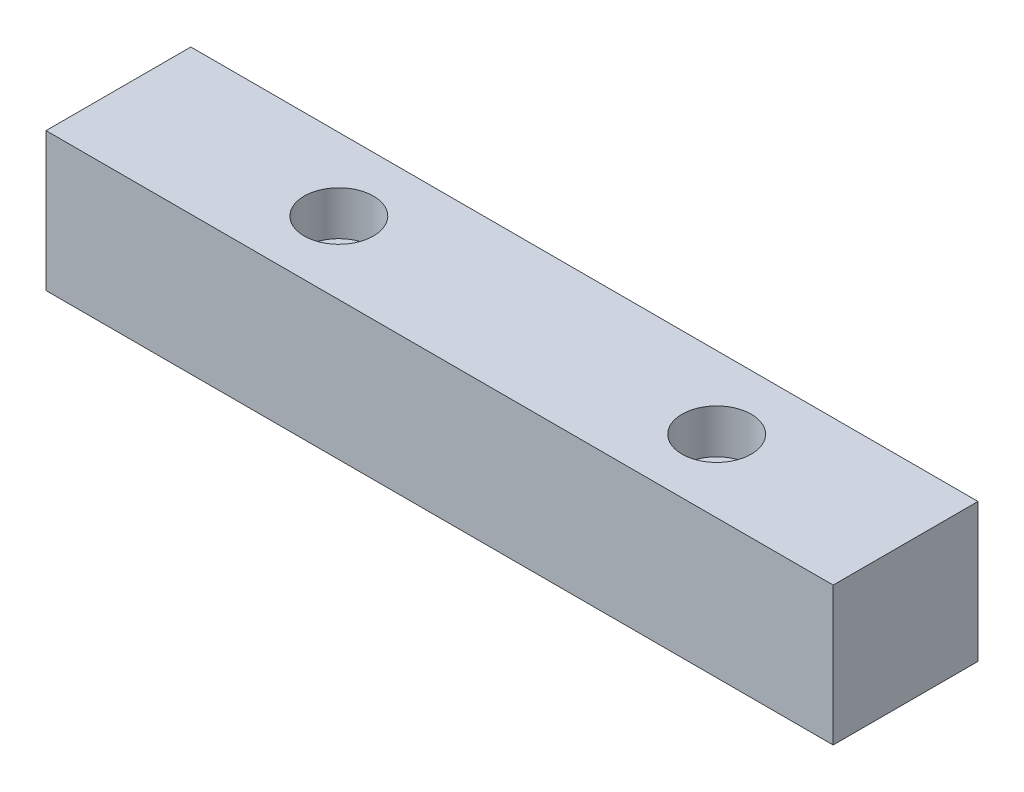
SolidWorks part; units mm, degrees
material "A3钢"
ref_plane "前视基准面" through (0, 0, 0) normal (0, 0, 1) x (1, 0, 0)
ref_plane "上视基准面" through (0, 0, 0) normal (0, 1, 0) x (1, 0, 0)
ref_plane "右视基准面" through (0, 0, 0) normal (1, 0, 0) x (0, 0, -1)
sketch "草图1" plane through (0, 0, 0) normal (1, 0, 0) x (0, 0, -1)
  line L1 (-11.5, -11) -> (11.5, -11)
  line L2 (-11.5, -11) -> (-11.5, 11)
  line L3 (-11.5, 11) -> (11.5, 11)
  line L4 (11.5, -11) -> (11.5, 11)
  line L5 (-11.5, -11) -> (11.5, 11) construction
  line L6 (-11.5, 11) -> (11.5, -11) construction
  point P0 (0, 0)
  dimension "D1" = 22
  dimension "D2" = 23
extrude "凸台-拉伸1" add sketch "草图1" along normal blind 125
hole_wizard "打孔尺寸(%根据)内六角圆柱头螺钉的类型1" positions "草图2" profile "草图3" counterbore size "M6" standard "GB" end condition through all
sketch "草图2" plane through (0, 11, 0) normal (0, 1, 0) x (1, 0, 0)
  line L0 (0, 11.5) -> (0, -11.5) construction
  line L1 (-4.5209, 0) -> (108.6401, 0) construction
  point P0 (35, 0)
  dimension "D1" = 35
sketch "草图3" plane through (35, 11, 0) normal (1, 0, 0) x (0, 0, 1)
  line L0 (0, 0) -> (0, 22)
  line L1 (0, 22) -> (3.25, 22)
  line L3 (3.25, 22) -> (3.25, 7)
  line L4 (3.25, 7) -> (5.5, 7)
  line L5 (5.5, 7) -> (5.5, 0)
  line L7 (5.5, 0) -> (0, 0)
  line L11 (0, -6.35) -> (0, 107.95) construction
  dimension "通孔孔直径" = 6.5
  dimension "通孔孔深度" = 22
  dimension "柱形沉头孔直径" = 11
  dimension "柱形沉头孔深度" = 7
pattern_linear "阵列(线性)2" count 2 spacing 60 along (1, 0, 0) of "打孔尺寸(%根据)内六角圆柱头螺钉的类型1"
